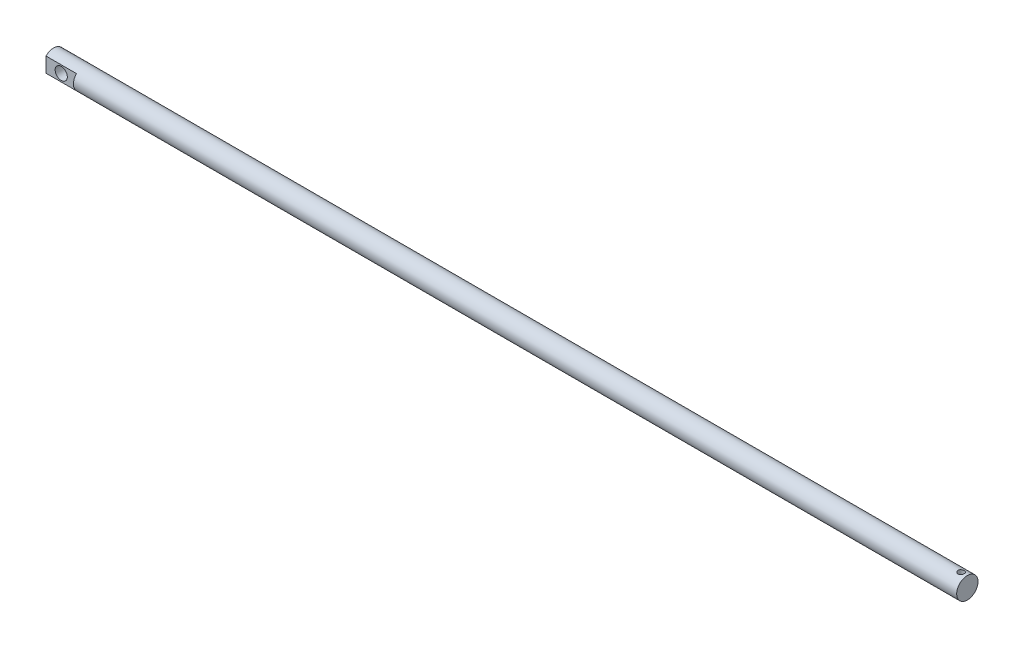
SolidWorks part; units mm, degrees
ref_plane "前视基准面" through (0, 0, 0) normal (0, 0, 1) x (1, 0, 0)
ref_plane "上视基准面" through (0, 0, 0) normal (0, 1, 0) x (1, 0, 0)
ref_plane "右视基准面" through (0, 0, 0) normal (1, 0, 0) x (0, 0, -1)
sketch "草图1" plane through (0, 0, 0) normal (1, 0, 0) x (0, 0, -1)
  circle A0 centre (0, 0) radius 7
  dimension "D1" = 14
extrude "凸台-拉伸1" add sketch "草图1" along normal blind 600
sketch "草图3" plane through (0, 0, 0) normal (-1, 0, 0) x (0, 0, 1)
  line L1 (-5, 10) -> (5, 10)
  line L2 (-5, 10) -> (-5, -10)
  line L3 (-5, -10) -> (5, -10)
  line L4 (5, 10) -> (5, -10)
  line L5 (-5, 10) -> (5, -10) construction
  line L6 (-5, -10) -> (5, 10) construction
  point P0 (0, 0)
  dimension "D1" = 20
  dimension "D2" = 10
extrude "切除-拉伸1" cut sketch "草图3" against normal blind 20 flip side to cut
sketch "草图4" plane through (0, 0, -5) normal (0, 0, -1) x (-1, 0, 0)
  line L0 (0, 4.899) -> (-20, 4.899) construction
  circle A0 centre (-10, 0) radius 4
  point P6 (-10, 4.899)
  dimension "D1" = 8
extrude "切除-拉伸3" cut sketch "草图4" against normal blind 20
sketch "草图5" plane through (-583.1382, 7, 1388.0261) normal (0, 1, 0) x (-1, 0, 0)
  circle A0 centre (-1179.1382, -1388.0261) radius 2 construction
  circle A1 centre (-1179.1382, -1388.0261) radius 2
extrude "切除-拉伸4" cut sketch "草图5" against normal through all
